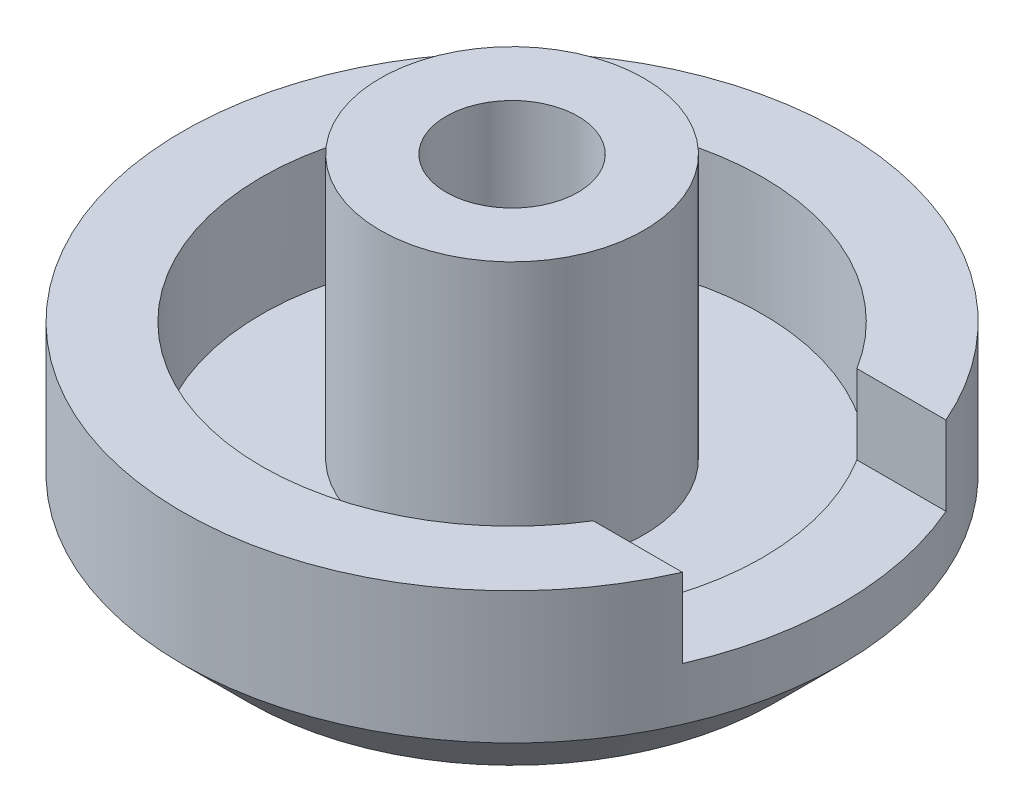
SolidWorks part; units mm, degrees
ref_plane "Front Plane" through (0, 0, 0) normal (0, 0, 1) x (1, 0, 0)
ref_plane "Top Plane" through (0, 0, 0) normal (0, 1, 0) x (1, 0, 0)
ref_plane "Right Plane" through (0, 0, 0) normal (1, 0, 0) x (0, 0, -1)
sketch "Sketch1" plane through (0, 0, 0) normal (0, 1, 0) x (1, 0, 0)
  circle A0 centre (0, 0) radius 5
  dimension "D1" = 10
extrude "Boss-Extrude1" add sketch "Sketch1" along normal blind 3
sketch "Sketch3" plane through (0, 3, 0) normal (0, 1, 0) x (1, 0, 0)
  circle A0 centre (0, 0) radius 3.8
  dimension "D1" = 7.6
extrude "Cut-Extrude1" cut sketch "Sketch3" against normal blind 1.8
sketch "Sketch4" plane through (0, 1.2, 0) normal (0, 1, 0) x (1, 0, 0)
  circle A0 centre (0, 0) radius 2
  dimension "D1" = 4
extrude "Boss-Extrude2" add sketch "Sketch4" along normal blind 4
sketch "Sketch5" plane through (0, 5.2, 0) normal (0, 1, 0) x (1, 0, 0)
  circle A0 centre (0, 0) radius 1
  dimension "D1" = 2
extrude "Cut-Extrude2" cut sketch "Sketch5" against normal blind 4
sketch "Sketch6" plane through (0, 3, 0) normal (0, 1, 0) x (1, 0, 0)
  line L1 (2, -2) -> (-2, -2) construction
  line L2 (2, -2) -> (2, 2) construction
  line L3 (2, 2) -> (-2, 2) construction
  line L4 (-2, -2) -> (-2, 2) construction
  line L5 (2, -2) -> (-2, 2) construction
  line L6 (2, 2) -> (-2, -2) construction
  line L7 (2, 2) -> (6, 2)
  line L8 (2, 2) -> (2, -2)
  line L9 (2, -2) -> (6, -2)
  line L10 (6, 2) -> (6, -2)
  point P0 (0, 0)
  dimension "D1" = 4
extrude "Cut-Extrude3" cut sketch "Sketch6" against normal blind 1.2
chamfer "Chamfer1" distance 1 angle 45 1 edges at (0, 0, 5)
